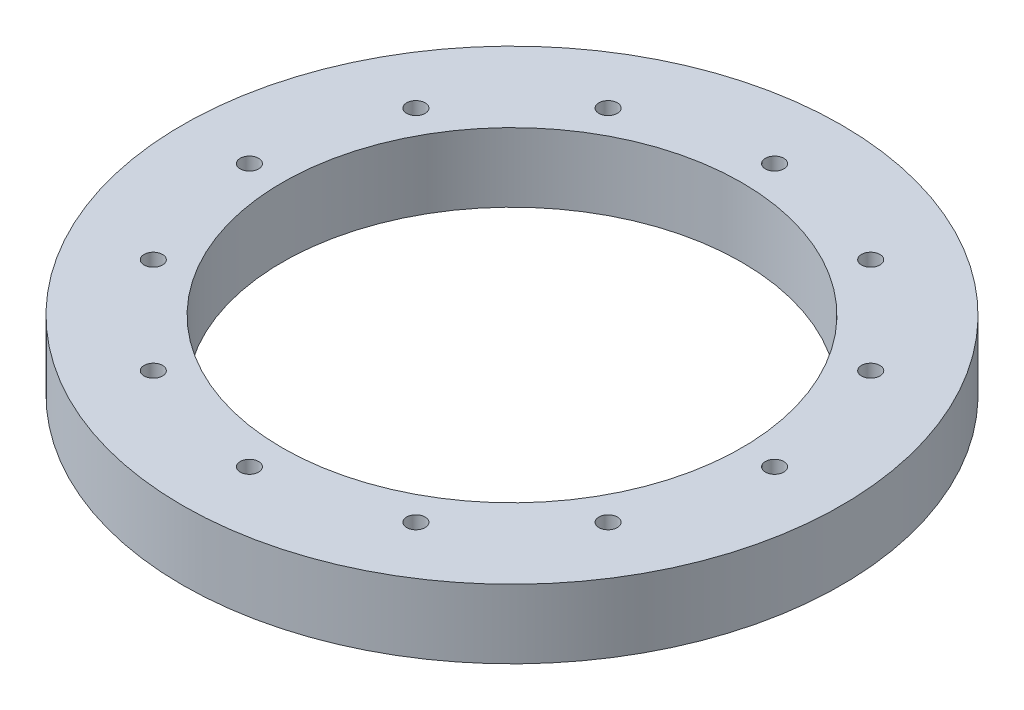
SolidWorks part; units mm, degrees
ref_plane "Front Plane" through (0, 0, 0) normal (0, 0, 1) x (1, 0, 0)
ref_plane "Top Plane" through (0, 0, 0) normal (0, 1, 0) x (1, 0, 0)
ref_plane "Right Plane" through (0, 0, 0) normal (1, 0, 0) x (0, 0, -1)
sketch "Sketch1" plane through (0, 0, 0) normal (0, 1, 0) x (1, 0, 0)
  circle A0 centre (0, 0) radius 101.6 construction
  circle A1 centre (0, 0) radius 127.508
  circle A2 centre (0, 0) radius 88.9
  circle A3 centre (0, 101.6) radius 3.5687
  circle A4 centre (50.8, 87.9882) radius 3.5687
  circle A5 centre (87.9882, 50.8) radius 3.5687
  circle A6 centre (101.6, 0) radius 3.5687
  circle A7 centre (87.9882, -50.8) radius 3.5687
  circle A8 centre (50.8, -87.9882) radius 3.5687
  circle A9 centre (0, -101.6) radius 3.5687
  circle A10 centre (-50.8, -87.9882) radius 3.5687
  circle A11 centre (-87.9882, -50.8) radius 3.5687
  circle A12 centre (-101.6, 0) radius 3.5687
  circle A13 centre (-87.9882, 50.8) radius 3.5687
  circle A14 centre (-50.8, 87.9882) radius 3.5687
  point P31 (0, 0)
  dimension "D1" = 203.2
  dimension "D2" = 255.016
  dimension "D3" = 177.8
  dimension "D4" = 7.1374
  dimension "D5" = 12
extrude "Boss-Extrude1" add sketch "Sketch1" along normal blind 26.67
sketch "Sketch2" plane through (0, 0, 0) normal (0, -1, 0) x (1, 0, 0)
  line L0 (101.6, 0) -> (-105.1687, 0) construction
  line L1 (-1.7843, 0) -> (-1.7843, -11.2198)
  circle A0 centre (-101.6, 0) radius 3.5687 construction
equation "\"A\"= 10.04in"
equation "\"B\"= 7in"
equation "\"C\"= 5.93in"
equation "\"D\"= .56in"
equation "\"E\"= 5.39in"
equation "\"F\"= 1.03in"
equation "\"D2@Sketch1\"=\"A\""
equation "\"D3@Sketch1\"=\"B\""
equation "\"BC\"=203.2"
equation "\"D1@Sketch1\"=\"BC\""
equation "\"diam_mount_hole\"=7.1374"
equation "\"D4@Sketch1\"=\"diam_mount_hole\""
equation "\"thick\"= 2.1in / 2"
equation "\"D1@Boss-Extrude1\"=\"thick\""
